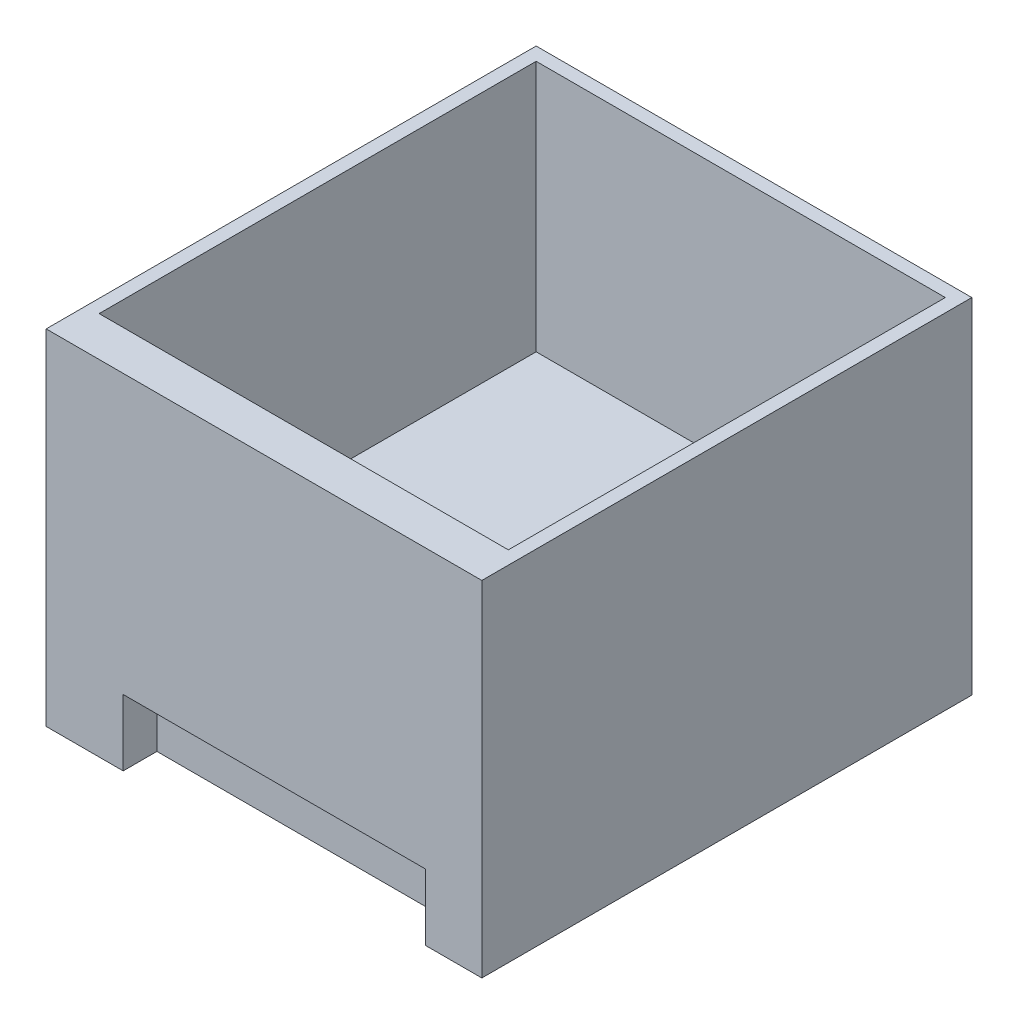
SolidWorks part; units mm, degrees
ref_plane "Plan de face" through (0, 0, 0) normal (0, 0, 1) x (1, 0, 0)
ref_plane "Plan de dessus" through (0, 0, 0) normal (0, 1, 0) x (1, 0, 0)
ref_plane "Plan de droite" through (0, 0, 0) normal (1, 0, 0) x (0, 0, -1)
sketch "Esquisse1" plane through (0, 0, 0) normal (0, 0, 1) x (1, 0, 0)
  line L1 (-98.7717, 47.4801) -> (230.2283, 47.4801)
  line L2 (-98.7717, 47.4801) -> (-98.7717, -212.5199)
  line L3 (-98.7717, -212.5199) -> (230.2283, -212.5199)
  line L4 (230.2283, 47.4801) -> (230.2283, -212.5199)
  dimension "D1" = 329
  dimension "D2" = 260
extrude "Boss.-Extru.1" add sketch "Esquisse1" against normal blind 370
sketch "Esquisse2" plane through (0, 47.4801, 0) normal (0, 1, 0) x (1, 0, 0)
  line L0 (230.2283, 0) -> (-98.7717, 0) construction
  line L1 (220.2283, 30) -> (-88.7717, 30)
  line L2 (220.2283, 30) -> (220.2283, 360)
  line L3 (220.2283, 360) -> (-88.7717, 360)
  line L4 (-88.7717, 30) -> (-88.7717, 360)
  line L5 (230.2283, 370) -> (230.2283, 0) construction
  line L6 (-98.7717, 370) -> (-98.7717, 0) construction
  line L7 (230.2283, 370) -> (-98.7717, 370) construction
  dimension "D1" = 30
  dimension "D2" = 10
  dimension "D3" = 10
  dimension "D4" = 10
extrude "Enlèv. mat.-Extru.1" cut sketch "Esquisse2" against normal blind 190
sketch "Esquisse11" plane through (0, -212.5199, 0) normal (0, -1, 0) x (-1, 0, 0)
  line L0 (98.7717, 0) -> (-230.2283, 0) construction
  line L1 (40.6245, 0) -> (-187.8558, 0)
  line L2 (40.6245, 0) -> (40.6245, 25.4709)
  line L3 (40.6245, 25.4709) -> (-187.8558, 25.4709)
  line L4 (-187.8558, 0) -> (-187.8558, 25.4709)
extrude "Enlèv. mat.-Extru.9" cut sketch "Esquisse11" against normal blind 50
